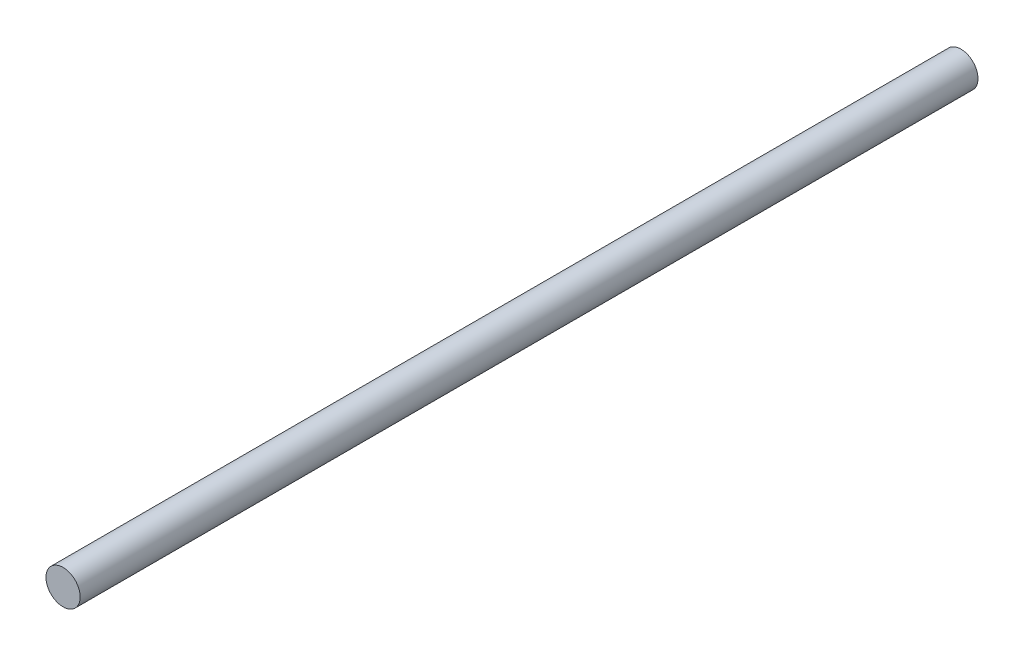
SolidWorks part; units mm, degrees
ref_plane "Plano frontal" through (0, 0, 0) normal (0, 0, 1) x (1, 0, 0)
ref_plane "Plano superior" through (0, 0, 0) normal (0, 1, 0) x (1, 0, 0)
ref_plane "Plano direito" through (0, 0, 0) normal (1, 0, 0) x (0, 0, -1)
sketch "Esboço1" plane through (0, 0, 0) normal (0, 0, 1) x (1, 0, 0)
  circle A0 centre (0, 0) radius 4
  dimension "D1" = 8
extrude "Ressalto-extrusão1" add sketch "Esboço1" along normal blind 210
